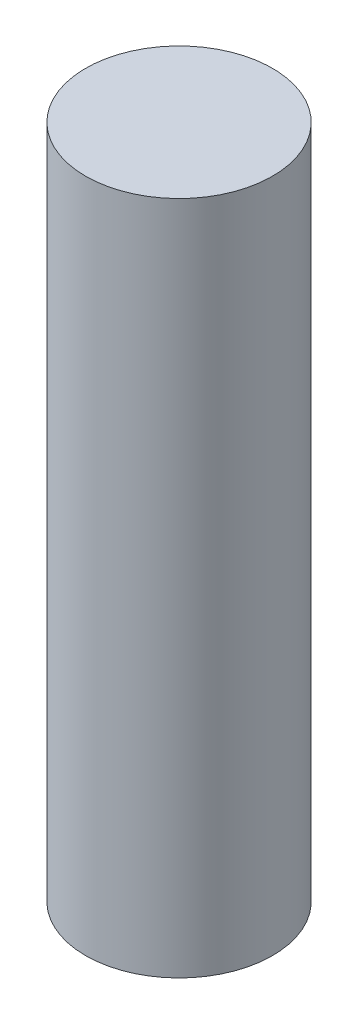
SolidWorks part; units mm, degrees
ref_plane "Plan de face" through (0, 0, 0) normal (0, 0, 1) x (1, 0, 0)
ref_plane "Plan de dessus" through (0, 0, 0) normal (0, 1, 0) x (1, 0, 0)
ref_plane "Plan de droite" through (0, 0, 0) normal (1, 0, 0) x (0, 0, -1)
sketch "Esquisse1" plane through (0, 0, 0) normal (0, 1, 0) x (1, 0, 0)
  circle A0 centre (0, 0) radius 9
  dimension "D1" = 18
extrude "Boss.-Extru.1" add sketch "Esquisse1" along normal blind 65
